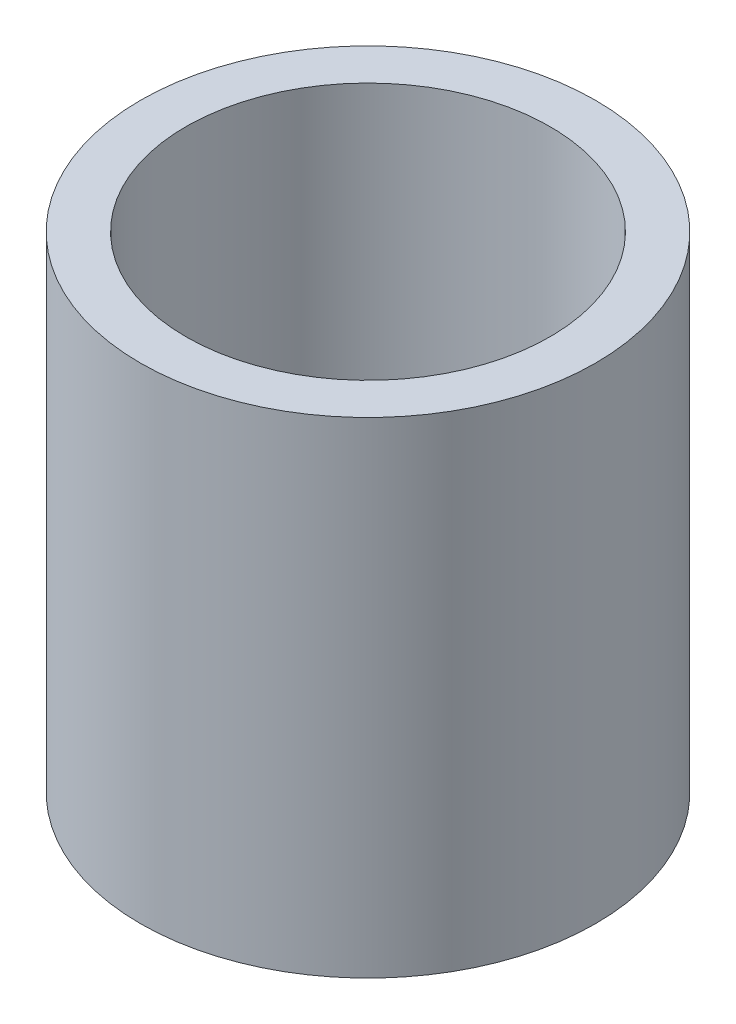
SolidWorks part; units mm, degrees
ref_plane "Front" through (0, 0, 0) normal (0, 0, 1) x (1, 0, 0)
ref_plane "Top" through (0, 0, 0) normal (0, 1, 0) x (1, 0, 0)
ref_plane "Right" through (0, 0, 0) normal (1, 0, 0) x (0, 0, -1)
sketch "Sketch1" plane through (0, 0, 0) normal (0, 1, 0) x (1, 0, 0)
  circle A0 centre (0, 0) radius 11.9062
  circle A1 centre (0, 0) radius 9.525
  dimension "D1" = 23.8125
  dimension "D2" = 19.05
extrude "Boss-Extrude1" add sketch "Sketch1" along normal blind 25.4
